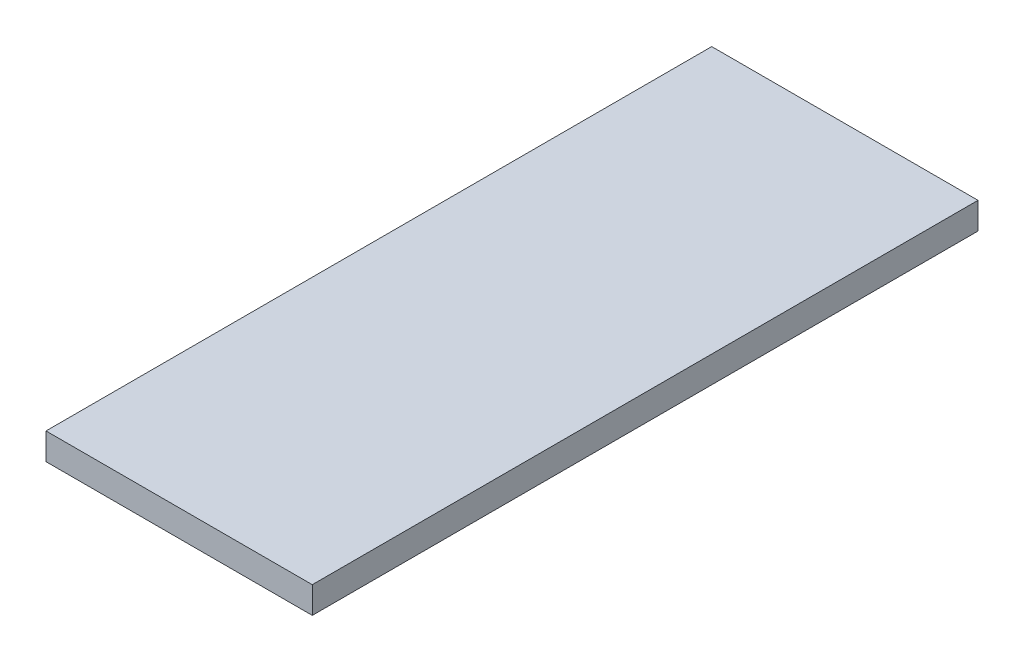
SolidWorks part; units mm, degrees
ref_plane "Front Plane" through (0, 0, 0) normal (0, 0, 1) x (1, 0, 0)
ref_plane "Top Plane" through (0, 0, 0) normal (0, 1, 0) x (1, 0, 0)
ref_plane "Right Plane" through (0, 0, 0) normal (1, 0, 0) x (0, 0, -1)
sketch "Sketch1" plane through (0, 0, 0) normal (0, 1, 0) x (1, 0, 0)
  line L1 (0, 0) -> (40, 0)
  line L2 (0, 0) -> (0, -100)
  line L3 (0, -100) -> (40, -100)
  line L4 (40, 0) -> (40, -100)
  dimension "D1" = 40
  dimension "D2" = 100
extrude "Boss-Extrude1" add sketch "Sketch1" along normal blind 4
